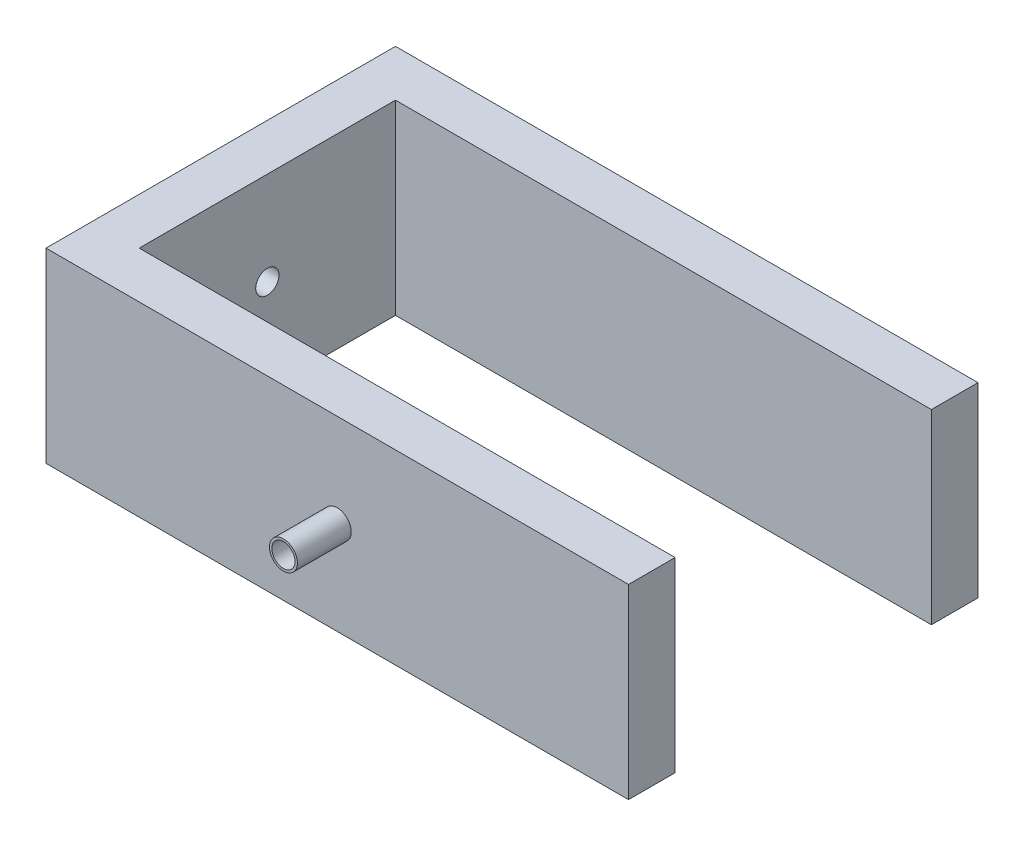
SolidWorks part; units mm, degrees
ref_plane "Front Plane" through (0, 0, 0) normal (0, 0, 1) x (1, 0, 0)
ref_plane "Top Plane" through (0, 0, 0) normal (0, 1, 0) x (1, 0, 0)
ref_plane "Right Plane" through (0, 0, 0) normal (1, 0, 0) x (0, 0, -1)
sketch "Sketch5" plane through (0, 0, 0) normal (1, 0, 0) x (0, 0, -1)
  line L0 (-37.5, 20) -> (37.5, -20) construction
  line L1 (-37.5, 20) -> (37.5, 20)
  line L2 (-37.5, 20) -> (-37.5, -20)
  line L3 (-37.5, -20) -> (37.5, -20)
  line L4 (37.5, 20) -> (37.5, -20)
  circle A0 centre (0, 0) radius 2.5
extrude "Boss-Extrude6" add sketch "Sketch5" along normal blind 10
sketch "Sketch6" plane through (0, 0, -37.5) normal (0, 0, -1) x (-1, 0, 0)
  line L0 (0, 20) -> (-125, -20) construction
  line L1 (0, 20) -> (-125, 20)
  line L2 (0, 20) -> (0, -20)
  line L3 (0, -20) -> (-125, -20)
  line L4 (-125, 20) -> (-125, -20)
extrude "Boss-Extrude7" add sketch "Sketch6" against normal blind 10
sketch "Sketch7" plane through (0, 0, 37.5) normal (0, 0, 1) x (1, 0, 0)
  line L0 (125, 20) -> (0, -20) construction
  line L1 (0, 20) -> (125, 20)
  line L2 (0, 20) -> (0, -20)
  line L3 (0, -20) -> (125, -20)
  line L4 (125, 20) -> (125, -20)
  line L5 (0, -20) -> (125, -20) construction
  line L6 (0, 20) -> (0, -20) construction
  line L7 (125, -20) -> (0, -20) construction
extrude "Boss-Extrude8" add sketch "Sketch7" against normal blind 10
sketch3d "3DSketch4" plane through (0, 0, 0) normal (0, 0, 1) x (1, 0, 0)
  dimension "D1" = 35
sketch "Sketch8" plane through (0, 0, -37.5) normal (0, 0, -1) x (-1, 0, 0)
  line L0 (0, -20) -> (-125, 20) construction
  circle A0 centre (-62.5, 0) radius 2.5
extrude "Boss-Extrude9" add sketch "Sketch8" along normal blind 11.55
sketch "Sketch10" plane through (0, 0, 37.5) normal (0, 0, -1) x (-1, 0, 0)
  line L0 (0, -20) -> (-125, 20) construction
  circle A0 centre (-62.5, 0) radius 3
  circle A2 centre (-62.5, 0) radius 2.5
extrude "Boss-Extrude10" add sketch "Sketch10" against normal blind 11.55
